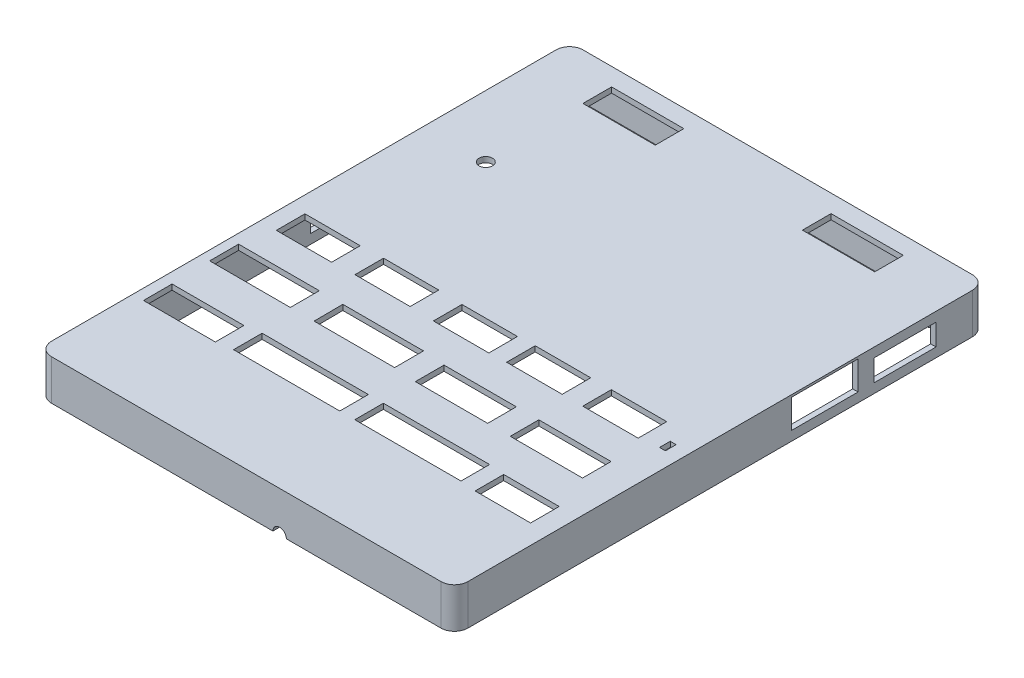
SolidWorks part; units mm, degrees
ref_plane "Front Plane" through (0, 0, 0) normal (0, 0, 1) x (1, 0, 0)
ref_plane "Top Plane" through (0, 0, 0) normal (0, 1, 0) x (1, 0, 0)
ref_plane "Right Plane" through (0, 0, 0) normal (1, 0, 0) x (0, 0, -1)
sketch "Sketch2" plane through (0, 0, 0) normal (0, 1, 0) x (1, 0, 0)
  line L0 (0, 0) -> (54.7068, 0) construction
  line L1 (54.7068, 0) -> (54.7068, 0.1279) construction
  line L2 (0, 0) -> (0, -73.5179) construction
  line L3 (0, -73.5179) -> (-1.2812, -73.5179) construction
  line L4 (-1.2812, -73.5179) -> (52.7304, -73.5179) construction
  line L5 (52.7304, -73.5179) -> (52.7304, -72.978) construction
  line L6 (0, 0) -> (-3.3977, 0) construction
  line L7 (-3.3977, 0) -> (-3.3977, -75.2568) construction
  line L8 (-3.3977, 0) -> (-3.3977, 2.7181) construction
  line L9 (-3.3977, 2.7181) -> (57.735, 2.7181) construction
  line L10 (57.735, 2.7181) -> (57.735, -75.2568) construction
  line L11 (57.735, -75.2568) -> (-3.3977, -75.2568) construction
  line L12 (-3.3977, 2.7181) -> (57.735, 2.7181) construction
  line L13 (57.735, 2.7181) -> (57.735, -75.2568) construction
  line L14 (57.735, -75.2568) -> (-3.3977, -75.2568) construction
  line L15 (-3.3977, -75.2568) -> (-3.3977, 2.7181) construction
  circle A0 centre (0, 0) radius 1.4094
  circle A1 centre (54.7068, 0.1279) radius 1.4094
  circle A2 centre (-1.2812, -73.5179) radius 1.4094
  circle A3 centre (52.7304, -72.978) radius 1.4094
  circle A4 centre (0, 0) radius 2.2
  circle A5 centre (54.7068, 0.1279) radius 2.2
  circle A6 centre (52.7304, -72.978) radius 2.2
  circle A7 centre (-1.2812, -73.5179) radius 2.2
  dimension "D1" = 4.4
sketch "Sketch3" plane through (0, 0, 0) normal (0, 1, 0) x (1, 0, 0)
  line L0 (-3.3977, 2.7181) -> (57.735, 2.7181)
  line L1 (57.735, 2.7181) -> (57.735, -75.2568)
  line L2 (57.735, -75.2568) -> (-3.3977, -75.2568)
  line L3 (-3.3977, -75.2568) -> (-3.3977, 2.7181)
  line L4 (-4.1977, 3.5181) -> (58.535, 3.5181)
  line L5 (58.535, 3.5181) -> (58.535, -76.0568)
  line L6 (58.535, -76.0568) -> (-4.1977, -76.0568)
  line L7 (-4.1977, -76.0568) -> (-4.1977, 3.5181)
  dimension "D1" = 0.8
sketch "Sketch4" plane through (0, 0, 0) normal (0, 1, 0) x (1, 0, 0)
  line L0 (-3.3977, 2.7181) -> (57.735, 2.7181)
  line L1 (57.735, 2.7181) -> (57.735, -75.2568)
  line L2 (57.735, -75.2568) -> (-3.3977, -75.2568)
  line L3 (-3.3977, -75.2568) -> (-3.3977, 2.7181)
extrude "Boss-Extrude8" add sketch "Sketch3" against normal blind 6
extrude "Boss-Extrude9" add sketch "Sketch2" against normal blind 4.6
extrude "Boss-Extrude11" add sketch "Sketch4" against normal blind 0.8
sketch "Sketch7" plane through (58.535, 0, 0) normal (1, 0, 0) x (0, 0, -1)
  line L0 (3.5181, 0) -> (-3.8989, 0) construction
  line L1 (-76.0568, 0) -> (3.5181, 0) construction
  line L2 (-3.8989, -4.6) -> (-3.8989, -2.1)
  line L3 (3.5181, 0) -> (-13.1259, 0) construction
  line L4 (-13.1259, -4.6) -> (-13.1259, -2.1)
  line L5 (3.5181, 0) -> (-15.4929, 0) construction
  line L6 (-13.1259, -2.1) -> (-3.8989, -2.1) construction
  line L7 (3.5181, 0) -> (-25.3989, 0) construction
  line L8 (-15.4929, -0.6) -> (-25.3989, -0.6) construction
  line L9 (3.5181, 0) -> (3.5181, -2.1) construction
  line L10 (3.5181, -6) -> (3.5181, 0) construction
  line L11 (-15.4929, -4.6) -> (-15.4929, -0.6)
  line L12 (-76.0568, -6) -> (-76.0568, 0) construction
  line L21 (3.5181, -6) -> (3.5181, -8.7) construction
  line L22 (3.5181, -8.7) -> (-76.0568, -8.7) construction
  line L31 (3.5181, -6) -> (3.5181, -4.6) construction
  line L32 (3.5181, -4.6) -> (-76.0568, -4.6) construction
  line L33 (-13.1259, -4.6) -> (-3.8989, -4.6)
  line L34 (-25.3989, -4.6) -> (-25.3989, -0.6)
  line L35 (-25.3989, -4.6) -> (-15.4929, -4.6)
  line L36 (-13.1259, -2.1) -> (-13.1259, -1.5)
  line L37 (-13.1259, -1.5) -> (-3.8989, -1.5) construction
  line L38 (-3.8989, -1.5) -> (-3.8989, -2.1)
  line L39 (-13.1259, -1.5) -> (-13.1259, -1.4)
  line L40 (-13.1259, -1.4) -> (-3.8989, -1.4)
  line L41 (-3.8989, -1.4) -> (-3.8989, -1.5)
  line L42 (-25.3989, -0.6) -> (-25.3989, -0.33)
  line L43 (-25.3989, -0.33) -> (-15.4929, -0.33)
  line L44 (-15.4929, -0.33) -> (-15.4929, -0.6)
extrude "Cut-Extrude2" cut sketch "Sketch7" against normal blind 4
sketch "Sketch8" plane through (-4.1977, 0, 0) normal (-1, 0, 0) x (0, 0, 1)
  line L0 (-3.5181, -6) -> (5.0819, -6) construction
  line L1 (-3.5181, -6) -> (76.0568, -6) construction
  line L3 (-3.5181, -6) -> (11.4319, -6) construction
  line L5 (-3.5181, -6) -> (14.3529, -6) construction
  line L7 (-3.5181, -6) -> (24.2589, -6) construction
  line L9 (-3.5181, -6) -> (28.1959, -6) construction
  line L11 (-3.5181, -6) -> (35.8169, -6) construction
  line L13 (-3.5181, -6) -> (-3.5181, -8.7) construction
  line L14 (-3.5181, -6) -> (-3.5181, 0) construction
  line L15 (-3.5181, -8.7) -> (76.0568, -8.7) construction
  line L16 (76.0568, -6) -> (76.0568, 0) construction
  line L23 (-3.5181, -6) -> (-3.5181, -4.6) construction
  line L24 (-3.5181, -4.6) -> (76.0568, -4.6) construction
  line L25 (5.0819, -4.6) -> (5.0819, -2.9)
  line L26 (11.4319, -4.6) -> (11.4319, -2.9)
  line L27 (5.0819, -2.9) -> (11.4319, -2.9)
  line L28 (5.0819, -4.6) -> (11.4319, -4.6)
  line L29 (14.4672, -4.6) -> (14.4672, -0.2)
  line L30 (24.2589, -4.6) -> (24.2589, -0.2)
  line L31 (24.2589, -0.2) -> (14.4672, -0.2)
  line L32 (14.4672, -4.6) -> (24.2589, -4.6)
  line L33 (28.1959, -4.6) -> (28.1959, -0.2)
  line L34 (28.1959, -0.2) -> (35.8169, -0.2)
  line L35 (35.8169, -0.2) -> (35.8169, -4.6)
  line L36 (35.8169, -4.6) -> (28.1959, -4.6)
extrude "Cut-Extrude3" cut sketch "Sketch8" against normal blind 1
sketch "Sketch10" plane through (0, 0, 0) normal (0, 1, 0) x (1, 0, 0)
  line L0 (58.535, 3.5181) -> (49.006, 3.5181) construction
  line L1 (58.535, 3.5181) -> (-4.1977, 3.5181) construction
  line L5 (38.147, 0.3821) -> (48.536, 0.3821) construction
  line L6 (37.957, 0.3821) -> (16.367, 0.3821) construction
  line L8 (15.897, 0.3821) -> (5.508, 0.3821) construction
  line L11 (58.535, 3.5181) -> (58.535, -37.8449) construction
  line L12 (58.535, -76.0568) -> (58.535, 3.5181) construction
  line L13 (58.535, -37.8449) -> (52.816, -37.8449) construction
  line L16 (52.366, -41.9949) -> (44.486, -41.9949) construction
  line L17 (44.486, -38.1449) -> (44.486, -41.9949)
  line L18 (58.535, -37.8449) -> (41.497, -37.8449) construction
  line L21 (33.167, -38.1449) -> (33.167, -41.9949)
  line L22 (33.167, -41.9949) -> (41.047, -41.9949) construction
  line L23 (58.535, -37.8449) -> (30.702, -37.8449) construction
  line L25 (30.292, -41.9949) -> (22.402, -41.9949) construction
  line L26 (22.402, -41.9949) -> (22.402, -38.2749)
  line L28 (58.535, -37.8449) -> (18.907, -37.8449) construction
  line L30 (18.457, -41.9949) -> (10.607, -41.9949) construction
  line L32 (10.607, -38.1449) -> (10.607, -41.9949)
  line L33 (58.535, -37.8449) -> (7.35, -37.8449) construction
  line L35 (6.9, -41.9949) -> (-0.95, -41.9949) construction
  line L36 (-0.95, -41.9949) -> (-0.95, -38.2749)
  line L38 (58.535, 3.5181) -> (58.535, -47.1159) construction
  line L41 (53.362, -51.2659) -> (43.785, -51.2659) construction
  line L42 (43.785, -51.2659) -> (43.785, -47.4159) construction
  line L43 (58.535, -47.1159) -> (39.735, -47.1159) construction
  line L46 (29.688, -47.4159) -> (29.688, -51.2659) construction
  line L47 (29.688, -51.2659) -> (39.265, -51.2659) construction
  line L48 (58.535, -47.1159) -> (25.675, -47.1159) construction
  line L50 (25.155, -47.1159) -> (13.775, -47.1159)
  line L51 (13.775, -47.1159) -> (13.775, -51.2659) construction
  line L52 (13.775, -51.2659) -> (25.155, -51.2659) construction
  line L53 (58.535, -47.1159) -> (10.144, -47.1159) construction
  line L55 (9.664, -51.2659) -> (-1.756, -51.2659) construction
  line L56 (-1.756, -51.2659) -> (-1.756, -47.1159) construction
  line L57 (-1.756, -47.1159) -> (9.664, -47.1159)
  line L58 (58.535, 3.5181) -> (58.535, -56.7679) construction
  line L64 (47.403, -57.0679) -> (55.013, -57.0679)
  line L69 (41.047, -38.1449) -> (33.167, -38.1449)
  line L70 (38.147, 0.3821) -> (38.147, -3.3859)
  line L71 (48.536, 0.3821) -> (48.536, -3.3859) construction
  line L72 (15.897, 0.3821) -> (15.897, -3.3859) construction
  line L73 (15.897, -3.3859) -> (5.508, -3.3859)
  line L74 (48.536, -3.3859) -> (38.147, -3.3859)
  line L75 (52.366, -38.1449) -> (52.366, -41.9949) construction
  line L76 (44.486, -38.1449) -> (52.366, -38.1449)
  line L77 (41.047, -38.1449) -> (41.047, -41.9949) construction
  line L78 (25.155, -47.1159) -> (25.155, -51.2659) construction
  line L79 (30.292, -38.2749) -> (22.402, -38.2749)
  line L80 (30.292, -38.2749) -> (30.292, -41.9949) construction
  line L81 (18.457, -38.1449) -> (18.457, -41.9949) construction
  line L82 (18.457, -38.1449) -> (10.607, -38.1449)
  line L83 (6.9, -38.2749) -> (6.9, -41.9949) construction
  line L84 (-0.95, -38.2749) -> (6.9, -38.2749)
  line L85 (53.362, -47.4159) -> (53.362, -51.2659) construction
  line L86 (53.362, -47.4159) -> (43.785, -47.4159)
  line L87 (39.265, -47.4159) -> (39.265, -51.2659) construction
  line L88 (29.688, -47.4159) -> (39.265, -47.4159)
  line L89 (9.664, -47.1159) -> (9.664, -51.2659) construction
  line L90 (53.362, -47.4159) -> (55.013, -47.4159) construction
  line L91 (44.754, -56.8379) -> (44.754, -60.9179) construction
  line L94 (47.403, -60.9179) -> (55.013, -60.9179) construction
  line L95 (55.013, -60.9179) -> (55.013, -57.0679) construction
  line L98 (29.276, -60.9179) -> (44.754, -60.9179) construction
  line L99 (29.006, -56.7679) -> (26.72, -56.7679) construction
  line L100 (26.72, -56.8379) -> (26.72, -60.9179) construction
  line L103 (11.24, -60.9179) -> (26.72, -60.9179) construction
  line L104 (11.12, -56.7679) -> (8.707, -56.7679) construction
  line L105 (8.707, -57.1979) -> (8.707, -60.9179) construction
  line L107 (-1.793, -57.1979) -> (-1.793, -60.9179)
  line L108 (-1.793, -60.9179) -> (8.707, -60.9179) construction
  line L109 (5.508, 0.3821) -> (5.508, -3.3859)
  line L111 (47.403, -57.0679) -> (47.403, -60.9179)
  line L112 (58.535, 3.5181) -> (58.535, -18.1599) construction
  line L114 (29.276, -56.8379) -> (29.276, -60.9179)
  line L115 (29.276, -56.8379) -> (44.754, -56.8379)
  line L116 (11.24, -56.8379) -> (11.24, -60.9179)
  line L117 (11.24, -56.8379) -> (26.72, -56.8379)
  line L118 (-1.793, -57.1979) -> (8.707, -57.1979)
  line L119 (58.535, -18.1599) -> (5.826, -18.1599) construction
  line L120 (5.508, 0.3821) -> (5.508, 0.8721)
  line L123 (15.897, 0.3821) -> (16.257, 0.3821) construction
  line L124 (56.2852, -41.9949) -> (55.5092, -41.9949)
  line L126 (5.508, 0.8721) -> (16.257, 0.8721)
  line L127 (55.5092, -40.4039) -> (55.5092, -41.9949)
  line L128 (55.5092, -40.4039) -> (56.3852, -40.4039)
  line L129 (56.3852, -40.4039) -> (56.3852, -41.9949)
  line L130 (56.3852, -41.9949) -> (56.2852, -41.9949)
  line L131 (16.257, 0.8721) -> (16.257, -3.3859)
  line L132 (16.257, -3.3859) -> (15.897, -3.3859)
  line L133 (38.147, 0.3821) -> (38.147, 0.8721)
  line L134 (48.536, 0.3821) -> (48.896, 0.3821) construction
  line L135 (38.147, 0.8721) -> (48.896, 0.8721)
  line L136 (48.896, 0.8721) -> (48.896, -3.3859)
  line L137 (48.896, -3.3859) -> (48.536, -3.3859)
  line L138 (6.9, -38.2749) -> (7.27, -38.2749)
  line L139 (-0.95, -41.9949) -> (-0.95, -42.5349)
  line L140 (-0.95, -42.5349) -> (7.27, -42.5349)
  line L141 (7.27, -42.5349) -> (7.27, -38.2749)
  line L142 (18.457, -38.1449) -> (18.817, -38.1449)
  line L143 (10.607, -41.9949) -> (10.607, -42.3949)
  line L144 (10.607, -42.3949) -> (18.817, -42.3949)
  line L145 (18.817, -42.3949) -> (18.817, -38.1449)
  line L146 (22.402, -41.9949) -> (22.402, -42.5249)
  line L147 (30.292, -38.2749) -> (30.652, -38.2749)
  line L148 (30.652, -38.2749) -> (30.652, -42.5249)
  line L149 (30.652, -42.5249) -> (22.402, -42.5249)
  line L150 (41.047, -38.1449) -> (41.427, -38.1449)
  line L151 (33.167, -41.9949) -> (33.167, -42.3949)
  line L152 (41.427, -38.1449) -> (41.427, -42.3949)
  line L153 (41.427, -42.3949) -> (33.167, -42.3949)
  line L154 (52.366, -38.1449) -> (52.726, -38.1449)
  line L155 (44.486, -41.9949) -> (44.486, -42.3949)
  line L156 (52.726, -38.1449) -> (52.726, -42.3949)
  line L157 (52.726, -42.3949) -> (44.486, -42.3949)
  line L158 (-1.756, -47.1159) -> (-1.976, -47.1159)
  line L159 (9.664, -47.1159) -> (10.024, -47.1159)
  line L160 (-1.756, -51.2659) -> (-1.756, -51.4259) construction
  line L161 (-1.976, -47.1159) -> (-1.976, -51.4259)
  line L162 (-1.976, -51.4259) -> (-1.756, -51.4259)
  line L163 (-1.756, -51.4259) -> (10.024, -51.4259)
  line L164 (10.024, -51.4259) -> (10.024, -47.1159)
  line L165 (13.775, -47.1159) -> (13.525, -47.1159)
  line L166 (25.155, -47.1159) -> (25.525, -47.1159)
  line L167 (13.775, -51.2659) -> (13.775, -51.4159) construction
  line L168 (13.525, -47.1159) -> (13.5527, -51.4159)
  line L169 (13.5527, -51.4159) -> (13.775, -51.4159)
  line L170 (13.775, -51.4159) -> (25.525, -51.4159)
  line L171 (25.525, -51.4159) -> (25.525, -47.1159)
  line L172 (29.688, -47.4159) -> (28.8764, -47.4159)
  line L173 (39.265, -47.4159) -> (39.625, -47.4159)
  line L174 (29.688, -51.2659) -> (29.688, -51.6759) construction
  line L175 (28.8764, -47.4159) -> (28.8764, -51.6759)
  line L176 (28.8764, -51.6759) -> (29.688, -51.6759)
  line L177 (29.688, -51.6759) -> (39.625, -51.6759)
  line L178 (39.625, -51.6759) -> (39.625, -47.4159)
  line L179 (43.785, -51.2659) -> (43.785, -51.6659) construction
  line L180 (53.362, -47.4159) -> (53.722, -47.4159)
  line L181 (43.785, -47.4159) -> (42.975, -47.4159)
  line L182 (42.975, -47.4159) -> (42.975, -51.6659)
  line L183 (42.975, -51.6659) -> (43.785, -51.6659)
  line L184 (43.785, -51.6659) -> (53.722, -51.6659)
  line L185 (53.722, -51.6659) -> (53.722, -47.4159)
  line L186 (-1.793, -60.9179) -> (-1.793, -61.4479)
  line L187 (8.707, -57.1979) -> (8.897, -57.1979)
  line L188 (8.897, -57.1979) -> (8.897, -61.4479)
  line L189 (8.897, -61.4479) -> (-1.793, -61.4479)
  line L190 (26.72, -56.8379) -> (27.04, -56.8379)
  line L191 (11.24, -60.9179) -> (11.24, -61.0879)
  line L192 (11.24, -61.0879) -> (27.04, -61.0879)
  line L193 (27.04, -61.0879) -> (27.04, -56.8379)
  line L194 (44.754, -56.8379) -> (45.074, -56.8379)
  line L195 (29.276, -60.9179) -> (29.276, -61.0879)
  line L196 (45.074, -56.8379) -> (45.074, -61.0879)
  line L197 (45.074, -61.0879) -> (29.276, -61.0879)
  line L198 (55.013, -57.0679) -> (55.653, -57.0679)
  line L199 (47.403, -60.9179) -> (47.403, -61.3179)
  line L200 (47.403, -61.3179) -> (55.653, -61.3179)
  line L201 (55.653, -61.3179) -> (55.653, -57.0679)
  circle A0 centre (5.826, -18.1599) radius 1
extrude "Cut-Extrude4" cut sketch "Sketch10" against normal blind 10
sketch "Sketch11" plane through (0, 0, 0) normal (0, 1, 0) x (1, 0, 0)
  line L0 (-4.1977, -76.0568) -> (-4.1977, -75.5268)
  line L1 (-4.1977, 3.5181) -> (-4.1977, -76.0568) construction
  line L2 (-4.1977, -75.5268) -> (58.535, -75.5268)
  line L3 (58.535, -76.0568) -> (58.535, 3.5181) construction
  line L4 (58.535, -75.5268) -> (58.535, -76.0568)
  line L5 (58.535, -76.0568) -> (-4.1977, -76.0568)
extrude "Cut-Extrude5" cut sketch "Sketch11" against normal blind 10
sketch "Sketch12" plane through (0, -6, 0) normal (0, -1, 0) x (1, 0, 0)
  line L0 (57.737, 75.5268) -> (57.735, 74.7268)
  line L1 (-4.1977, 75.5268) -> (58.535, 75.5268) construction
  line L2 (57.735, 75.2568) -> (57.735, 25.3989) construction
  line L3 (57.735, 74.7268) -> (-3.3977, 74.7268)
  line L4 (-3.3977, -2.7181) -> (-3.3977, 75.2568) construction
  line L5 (-3.3977, 74.7268) -> (-3.3977, 75.2568)
  line L6 (57.737, 75.5268) -> (-3.3977, 75.5268)
  line L7 (-3.3977, 75.5268) -> (-3.3977, 74.7268)
  line M6 (-3.3977, -2.7181) -> (-3.3977, 75.2568)
  line M7 (-3.3977, 75.2568) -> (57.735, 75.2568)
  line M8 (57.735, 75.2568) -> (57.735, -2.7181)
extrude "Boss-Extrude12" add sketch "Sketch12" against normal up to surface (6 mm away) contours L3 M8 M7 M6 up to face at (37.297, 0, 40.2699)
sketch "Sketch15" plane through (0, -6, 0) normal (0, -1, 0) x (1, 0, 0)
  line L0 (-3.3977, 74.7268) -> (-2.5877, 74.7268)
  line L2 (57.735, 74.7268) -> (-3.3977, 74.7268) construction
  line L3 (-2.5877, 74.7268) -> (-2.5877, -2.7181)
  line L4 (57.735, -2.7181) -> (-3.3977, -2.7181) construction
  line L5 (-2.5877, -2.7181) -> (-2.5877, -3.5181)
  line L6 (58.535, -3.5181) -> (-4.1977, -3.5181) construction
  line L7 (-2.5877, -3.5181) -> (-3.3977, -3.5181)
  line L8 (-3.3977, -3.5181) -> (-3.3977, 74.7268)
extrude "Boss-Extrude14" add sketch "Sketch15" against normal up to surface (6 mm away) up to face at (27.1687, 0, 36.0043)
sketch "Sketch16" plane through (0, -6, 0) normal (0, -1, 0) x (1, 0, 0)
  line L0 (-4.1977, 75.5268) -> (-3.3897, 75.5268)
  line L1 (-4.1977, 75.5268) -> (58.535, 75.5268) construction
  line L2 (-3.3897, 75.5268) -> (-3.3897, -3.5181)
  line L3 (58.535, -3.5181) -> (-4.1977, -3.5181) construction
  line L4 (-3.3897, -3.5181) -> (-4.1977, -3.5181)
  line L5 (-4.1977, -3.5181) -> (-4.1977, 75.5268)
extrude "Cut-Extrude6" cut sketch "Sketch16" against normal blind 10
sketch "Sketch17" plane through (0, 0, 75.5268) normal (0, 0, 1) x (1, 0, 0)
  line L0 (58.535, -6) -> (32.535, -6) construction
  line L1 (-3.3897, -6) -> (58.535, -6) construction
  line L2 (31.535, -6) -> (33.535, -6)
  arc A0 (31.535, -6) -> (33.535, -6) centre (32.535, -6) cw
extrude "Cut-Extrude7" cut sketch "Sketch17" against normal blind 10 contours L2 A0
sketch "Sketch20" plane through (-3.3897, 0, 0) normal (-1, 0, 0) x (0, 0, 1)
  line L0 (-3.5181, -6) -> (-3.5181, -4.6) construction
  line L1 (-3.5181, 0) -> (-3.5181, -6) construction
  line L2 (-3.5181, -4.6) -> (75.5268, -4.6) construction
  line L3 (75.5268, 0) -> (75.5268, -6) construction
  line L4 (-3.5181, -4.6) -> (5.0819, -4.6) construction
  line L5 (5.0819, -4.6) -> (5.0819, -2.9)
  line L6 (5.0819, -2.9) -> (11.4319, -2.9) construction
  line L7 (11.4319, -2.9) -> (11.4319, -4.6)
  line L8 (11.4319, -4.6) -> (5.0819, -4.6)
  line L9 (-3.5181, -4.6) -> (14.4719, -4.6) construction
  line L10 (14.4719, -4.6) -> (14.4719, -0.3)
  line L11 (14.4719, -0.3) -> (24.2635, -0.3)
  line L12 (24.2635, -0.3) -> (24.2635, -4.6)
  line L13 (24.2635, -4.6) -> (14.4719, -4.6)
  line L14 (-3.5181, -4.6) -> (28.1919, -4.6) construction
  line L15 (28.1919, -4.6) -> (28.1919, -0.3)
  line L16 (28.1919, -0.3) -> (35.8129, -0.3)
  line L17 (35.8129, -0.3) -> (35.8129, -4.6)
  line L18 (35.8129, -4.6) -> (28.1919, -4.6)
  line L19 (5.0819, -2.9) -> (5.0819, -2.75)
  line L20 (5.0819, -2.75) -> (11.4319, -2.75)
  line L21 (11.4319, -2.75) -> (11.4319, -2.9)
extrude "Cut-Extrude9" cut sketch "Sketch20" against normal blind 4
fillet "Fillet1" radius 2 4 edges at (-3.3897, -3, 75.5268) (58.535, -3, 75.5268) (58.535, -3, -3.5181) (-3.3897, -3, -3.5181)
